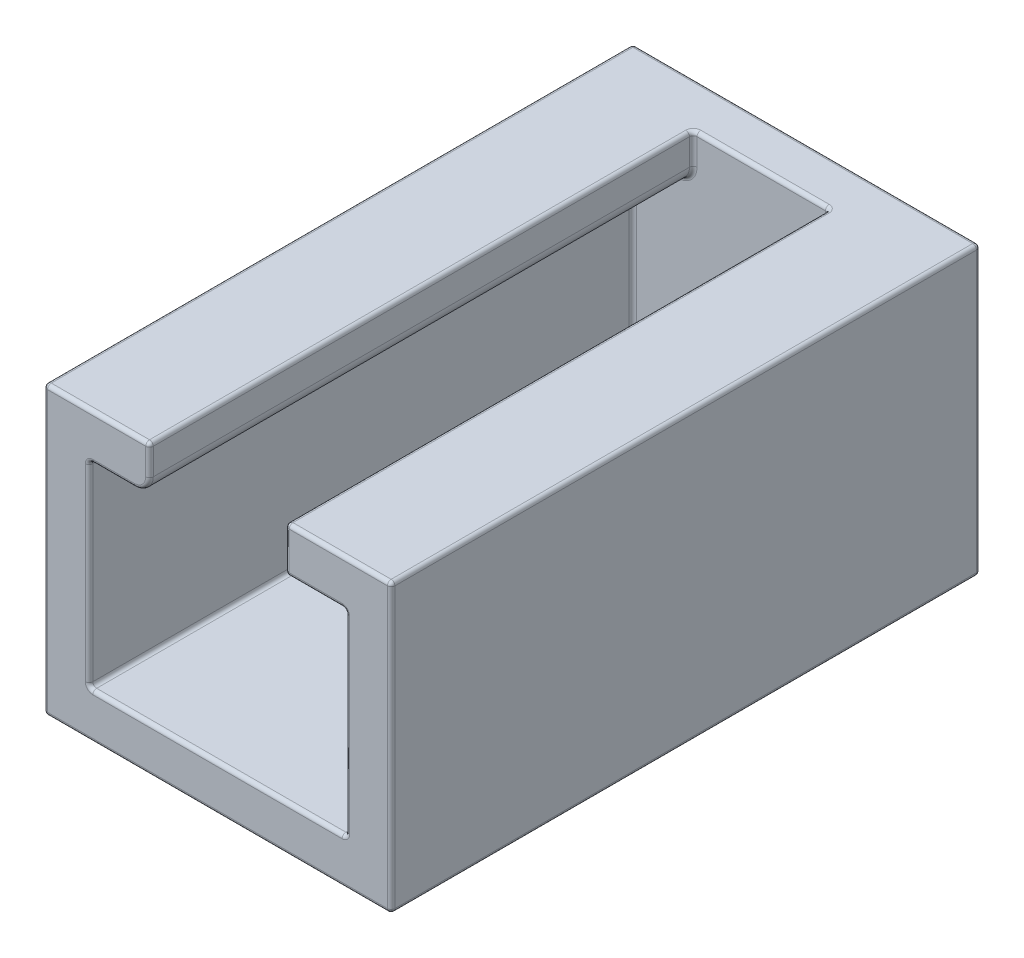
SolidWorks part; units mm, degrees
material "ABS"
ref_plane "Face" through (0, 0, 0) normal (0, 0, 1) x (1, 0, 0)
ref_plane "Dessus" through (0, 0, 0) normal (0, 1, 0) x (1, 0, 0)
ref_plane "Droite" through (0, 0, 0) normal (1, 0, 0) x (0, 0, -1)
sketch "Esquisse1" plane through (0, 0, 0) normal (0, 0, 1) x (1, 0, 0)
  line L28 (0, 0) -> (23, 0)
  line L29 (23, 0) -> (23, 3)
  line L30 (23, 3) -> (23, 19)
  line L31 (23, 19) -> (16, 19)
  line L32 (16, 19) -> (16, 16)
  line L33 (16, 16) -> (20, 16)
  line L34 (20, 16) -> (20, 3)
  line L35 (20, 3) -> (3, 3)
  line L36 (3, 3) -> (3, 16)
  line L37 (3, 16) -> (7, 16)
  line L38 (7, 16) -> (7, 19)
  line L39 (7, 19) -> (0, 19)
  line L40 (0, 19) -> (0, 3)
  line L41 (0, 3) -> (0, 0)
  dimension "D1" = 23
  dimension "D2" = 3
  dimension "D3" = 3
  dimension "D4" = 17
  dimension "D5" = 16
  dimension "D6" = 13
  dimension "D7" = 13
  dimension "D8" = 7
  dimension "D9" = 7
  dimension "D10" = 3
  dimension "D11" = 3
  dimension "D12" = 3
extrude "Boss.-Extru.1" add sketch "Esquisse1" along normal blind 36
sketch "Esquisse2" plane through (0, 0, 0) normal (0, 0, 1) x (1, 0, 0)
  line L1 (23, 19) -> (0, 19)
  line L2 (23, 19) -> (23, 0)
  line L3 (23, 0) -> (0, 0)
  line L4 (0, 19) -> (0, 0)
extrude "Boss.-Extru.2" add sketch "Esquisse2" against normal blind 3
fillet "Congé1" radius 1 1 edges at (7, 16, 18)
fillet "Congé2" radius 0.25 37 edges at (16, 17.5, 0) (7, 18, 0) (6.7071, 16.2929, 0) (6.7071, 16.2929, 36) (4.5, 16, 36) (0, 9.5, 36) (3.5, 19, 36) (0, 19, 16.5) (11.5, 19, -3) (0, 9.5, -3) (23, 9.5, -3) (23, 9.5, 36) (23, 19, 16.5) (16, 17.5, 36) (16, 19, 18) (11.5, 19, 0) (4.5, 16, 0) (18, 16, 0) (18, 16, 36) (19.5, 19, 36) (16, 16, 18) (20, 16, 18) (20, 9.5, 36) (20, 3, 18) (20, 9.5, 0) (11.5, 3, 0) (3, 9.5, 0) (3, 16, 18) (7, 18, 36) (7, 19, 18) (3, 3, 18) (3, 9.5, 36) (11.5, 3, 36) (11.5, 0, 36) (0, 0, 16.5) (11.5, 0, -3) (23, 0, 16.5)
